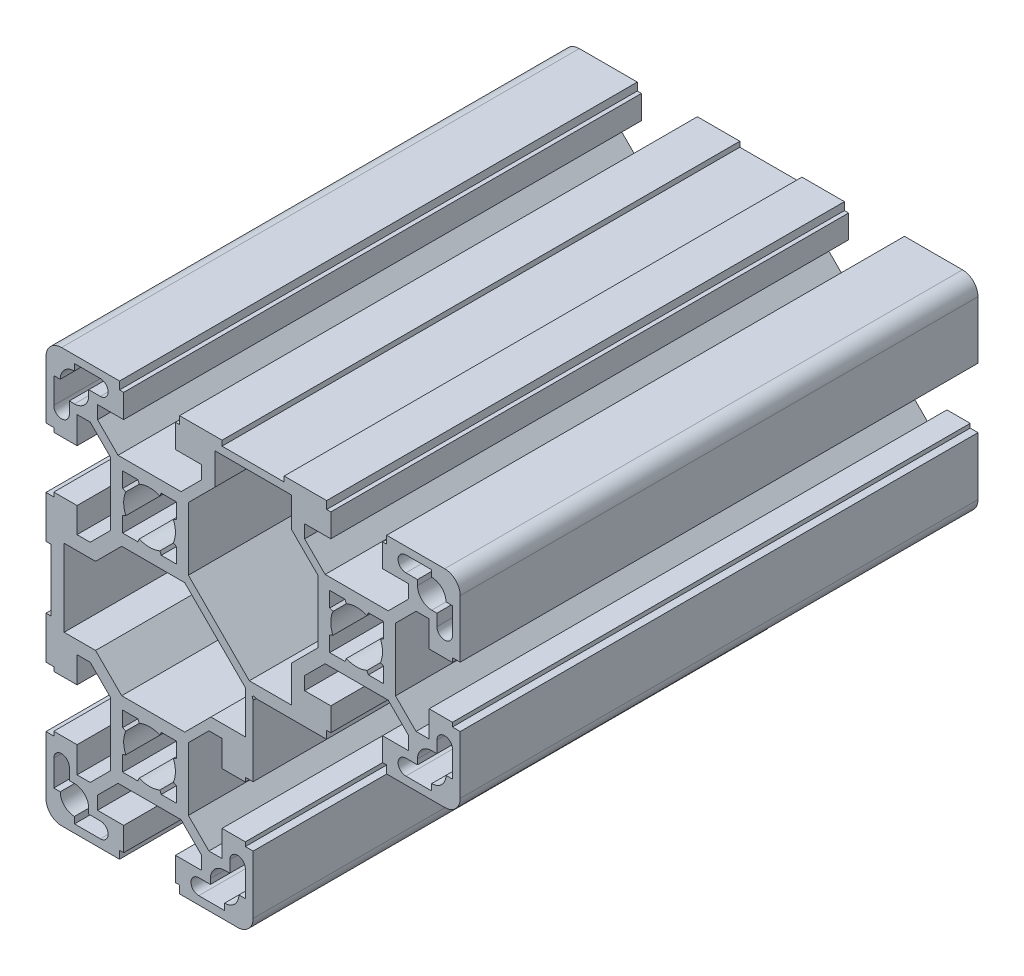
SolidWorks part; units mm, degrees
material "6063-T6"
ref_plane "Front Plane" through (0, 0, 0) normal (0, 0, 1) x (1, 0, 0)
ref_plane "Top Plane" through (0, 0, 0) normal (0, 1, 0) x (1, 0, 0)
ref_plane "Right Plane" through (0, 0, 0) normal (1, 0, 0) x (0, 0, -1)
sketch "Sketch1" plane through (0, 0, 0) normal (0, 0, 1) x (1, 0, 0)
  line L0 (25.9999, 38.9999) -> (14, 38.9999)
  line L1 (19.812, 0) -> (20.0684, 0.2563)
  line L2 (20, -0.5164) -> (19.812, 0)
  line L3 (18.5, -14.1316) -> (20, -14.1316)
  line L4 (20, -25.7315) -> (18.5, -25.7315)
  line L5 (27.4499, 2.3916) -> (19.2677, 2.3916)
  line L6 (12.6384, 37.5406) -> (27.4499, 37.5406)
  line L7 (44.9999, 1.5684) -> (45.7999, 1.5684)
  line L8 (50.0499, 6.0684) -> (44.9999, 6.0684)
  line L9 (44.9999, 33.9999) -> (50.0499, 33.9999)
  line L10 (45.7999, 38.4999) -> (44.9999, 38.4999)
  line L11 (46.0857, 27.4999) -> (33.9141, 27.4999)
  line L12 (33.9141, 12.5684) -> (46.0857, 12.5684)
  line L13 (53.9999, 30.1183) -> (53.9999, 25.0684)
  line L14 (58.4999, 25.0684) -> (58.4999, 25.8684)
  line L15 (47.4999, 13.9826) -> (47.4999, 26.1541)
  line L16 (57.2499, 34.5683) -> (58.4999, 34.5683)
  line L17 (59.9999, 25.8684) -> (59.9999, 36.9999)
  line L18 (58.4999, 34.5683) -> (58.4999, 29.5683)
  line L19 (58.4999, 25.8684) -> (59.9999, 25.8684)
  line L20 (54.4999, 38.5683) -> (54.4999, 37.3183)
  line L21 (56.9999, 39.9999) -> (45.7999, 39.9999)
  line L22 (49.4999, 38.5683) -> (54.4999, 38.5683)
  line L23 (45.7999, 39.9999) -> (45.7999, 38.4999)
  line L24 (51.4641, 30.1183) -> (53.9999, 30.1183)
  line L25 (51.7499, 35.5683) -> (49.4999, 35.5683)
  line L26 (55.4999, 29.5683) -> (55.4999, 31.8183)
  line L27 (55.4999, 31.8183) -> (54.4999, 31.8183)
  line L28 (51.7499, 34.5683) -> (51.7499, 35.5683)
  line L29 (50.0499, 33.9999) -> (50.0499, 31.4642)
  line L30 (50.0499, 31.4642) -> (46.0857, 27.4999)
  line L31 (47.4999, 26.1541) -> (51.4641, 30.1183)
  line L32 (58.4999, 15.0684) -> (53.9999, 15.0684)
  line L33 (58.4999, 5.5684) -> (57.2499, 5.5684)
  line L34 (53.9999, 25.0684) -> (58.4999, 25.0684)
  line L35 (59.9999, 3.0684) -> (59.9999, 14.2684)
  line L36 (59.9999, 14.2684) -> (58.4999, 14.2684)
  line L37 (58.4999, 14.2684) -> (58.4999, 15.0684)
  line L38 (58.4999, 10.5684) -> (58.4999, 5.5684)
  line L39 (51.4641, 10.0184) -> (47.4999, 13.9826)
  line L40 (53.9999, 15.0684) -> (53.9999, 10.0184)
  line L41 (53.9999, 10.0184) -> (51.4641, 10.0184)
  line L42 (45.7999, 0.0684) -> (56.9999, 0.0684)
  line L43 (54.4999, 1.5684) -> (49.4999, 1.5684)
  line L44 (49.4999, 4.5684) -> (51.7499, 4.5684)
  line L45 (54.4999, 8.3184) -> (55.4999, 8.3184)
  line L46 (55.4999, 8.3184) -> (55.4999, 10.5684)
  line L47 (51.7499, 4.5684) -> (51.7499, 5.5684)
  line L48 (54.4999, 2.8184) -> (54.4999, 1.5684)
  line L49 (50.0499, 8.6042) -> (50.0499, 6.0684)
  line L50 (46.0857, 12.5684) -> (50.0499, 8.6042)
  line L51 (45.7999, 1.5684) -> (45.7999, 0.0684)
  line L52 (27.4499, 31.7345) -> (32.4999, 26.6845)
  line L53 (34.1999, 39.9999) -> (25.9999, 39.9999)
  line L54 (29.9499, 33.9999) -> (34.9999, 33.9999)
  line L55 (33.9141, 27.4999) -> (29.9499, 31.4642)
  line L56 (34.9999, 33.9999) -> (34.9999, 38.4999)
  line L57 (44.9999, 38.4999) -> (44.9999, 33.9999)
  line L58 (34.9999, 38.4999) -> (34.1999, 38.4999)
  line L59 (34.1999, 38.4999) -> (34.1999, 39.9999)
  line L60 (25.9999, 39.9999) -> (25.9999, 38.9999)
  line L61 (29.9499, 31.4642) -> (29.9499, 33.9999)
  line L62 (27.4499, 37.5406) -> (27.4499, 31.7345)
  line L63 (29.9499, 8.6042) -> (33.9141, 12.5684)
  line L64 (34.9999, 6.0684) -> (29.9499, 6.0684)
  line L65 (20.5847, 0.0684) -> (34.1999, 0.0684)
  line L66 (41.9931, 24.6539) -> (42.2602, 25.2684)
  line L67 (45.1999, 22.3286) -> (44.5854, 22.0616)
  line L68 (42.2602, 25.2684) -> (45.1999, 25.2684)
  line L69 (45.1999, 25.2684) -> (45.1999, 22.3286)
  line L70 (42.2602, 14.8684) -> (41.9931, 15.4828)
  line L71 (45.1999, 17.8081) -> (45.1999, 14.8684)
  line L72 (44.5854, 18.0752) -> (45.1999, 17.8081)
  line L73 (45.1999, 14.8684) -> (42.2602, 14.8684)
  line L74 (34.7999, 25.2684) -> (37.7396, 25.2684)
  line L75 (37.7396, 25.2684) -> (38.0067, 24.6539)
  line L76 (35.4144, 22.0616) -> (34.7999, 22.3286)
  line L77 (34.7999, 22.3286) -> (34.7999, 25.2684)
  line L78 (37.7396, 14.8684) -> (34.7999, 14.8684)
  line L79 (38.0067, 15.4828) -> (37.7396, 14.8684)
  line L80 (34.7999, 14.8684) -> (34.7999, 17.8081)
  line L81 (34.7999, 17.8081) -> (35.4144, 18.0752)
  line L82 (44.9999, 6.0684) -> (44.9999, 1.5684)
  line L83 (34.9999, 1.5684) -> (34.9999, 6.0684)
  line L84 (34.1999, 1.5684) -> (34.9999, 1.5684)
  line L85 (34.1999, 0.0684) -> (34.1999, 1.5684)
  line L86 (32.4999, 14.5129) -> (27.4499, 9.4629)
  line L87 (32.4999, 26.6845) -> (32.4999, 14.5129)
  line L88 (29.9499, 6.0684) -> (29.9499, 8.6042)
  line L89 (27.4499, 9.4629) -> (27.4499, 2.3916)
  line L90 (20.0684, 0.2563) -> (20.5847, 0.0684)
  line L91 (20, -14.1316) -> (20, -0.5164)
  line L92 (20, -36.9999) -> (20, -25.7315)
  line L93 (-19, 6.0684) -> (-19, -5.9316)
  line L94 (18.5606, 0.8006) -> (18.5606, -7.3816)
  line L95 (-16.5, -7.3816) -> (-16.5, 7.5184)
  line L96 (-10.4287, 7.5184) -> (-5.3787, 12.5684)
  line L97 (-10.05, 33.9315) -> (-5, 33.9315)
  line L98 (-5, 38.4999) -> (-5.8, 38.4999)
  line L99 (6.0858, 27.4315) -> (-6.0858, 27.4315)
  line L100 (7.5, 26.3309) -> (12.6384, 31.4693)
  line L101 (10.05, 31.3957) -> (6.0858, 27.4315)
  line L102 (5, 33.9315) -> (10.05, 33.9315)
  line L103 (14, 39.9999) -> (5.8, 39.9999)
  line L104 (14, 38.9999) -> (14, 39.9999)
  line L105 (10.05, 33.9315) -> (10.05, 31.3957)
  line L106 (12.6384, 31.4693) -> (12.6384, 37.5406)
  line L107 (-5, 33.9315) -> (-5, 38.4999)
  line L108 (5, 38.4999) -> (5, 33.9315)
  line L109 (5.8, 38.4999) -> (5, 38.4999)
  line L110 (5.8, 39.9999) -> (5.8, 38.4999)
  line L111 (6.7929, 12.5684) -> (18.5606, 0.8006)
  line L112 (19.2677, 2.3916) -> (7.5, 14.1594)
  line L113 (7.5, 14.1594) -> (7.5, 26.3309)
  line L114 (2.2603, 25.2684) -> (5.2, 25.2684)
  line L115 (5.2, 22.3286) -> (4.5855, 22.0616)
  line L116 (5.2, 25.2684) -> (5.2, 22.3286)
  line L117 (1.9932, 24.6539) -> (2.2603, 25.2684)
  line L118 (5.2, 14.8684) -> (2.2603, 14.8684)
  line L119 (5.2, 17.8081) -> (5.2, 14.8684)
  line L120 (4.5855, 18.0752) -> (5.2, 17.8081)
  line L121 (2.2603, 14.8684) -> (1.9932, 15.4828)
  line L122 (-2.2603, 25.2684) -> (-1.9932, 24.6539)
  line L123 (-4.5855, 22.0616) -> (-5.2, 22.3286)
  line L124 (-5.2, 25.2684) -> (-2.2603, 25.2684)
  line L125 (-5.2, 22.3286) -> (-5.2, 25.2684)
  line L126 (-1.9932, 15.4828) -> (-2.2603, 14.8684)
  line L127 (-5.2, 14.8684) -> (-5.2, 17.8081)
  line L128 (-5.2, 17.8081) -> (-4.5855, 18.0752)
  line L129 (-2.2603, 14.8684) -> (-5.2, 14.8684)
  line L130 (-5.3787, 12.5684) -> (6.7929, 12.5684)
  line L131 (-18.5, 25.8684) -> (-18.5, 25.0684)
  line L132 (-14, 25.0684) -> (-14, 30.2951)
  line L133 (-7.5, 26.3309) -> (-7.5, 14.1594)
  line L134 (-18.5, 34.5683) -> (-17.25, 34.5683)
  line L135 (-14.5, 37.3183) -> (-14.5, 38.5683)
  line L136 (-5.8, 39.9999) -> (-17, 39.9999)
  line L137 (-14.5, 38.5683) -> (-9.5, 38.5683)
  line L138 (-5.8, 38.4999) -> (-5.8, 39.9999)
  line L139 (-14, 30.2951) -> (-11.4642, 30.2951)
  line L140 (-9.5, 35.5683) -> (-11.75, 35.5683)
  line L141 (-10.05, 31.3957) -> (-10.05, 33.9315)
  line L142 (-6.0858, 27.4315) -> (-10.05, 31.3957)
  line L143 (-11.4642, 30.2951) -> (-7.5, 26.3309)
  line L144 (-15.5, 31.8183) -> (-15.5, 29.5683)
  line L145 (-14.5, 31.8183) -> (-15.5, 31.8183)
  line L146 (-11.75, 35.5683) -> (-11.75, 34.5683)
  line L147 (-20, 36.9999) -> (-20, 25.8684)
  line L148 (-18.5, 29.5683) -> (-18.5, 34.5683)
  line L149 (-20, 25.8684) -> (-18.5, 25.8684)
  line L150 (-14, 15.0684) -> (-18.5, 15.0684)
  line L151 (-18.5, 25.0684) -> (-14, 25.0684)
  line L152 (-14, 10.1952) -> (-14, 15.0684)
  line L153 (-7.5, 14.1594) -> (-11.4642, 10.1952)
  line L154 (-11.4642, 10.1952) -> (-14, 10.1952)
  line L155 (-16.5, 7.5184) -> (-10.4287, 7.5184)
  line L156 (-20, 14.2684) -> (-20, 6.0684)
  line L157 (-18.5, 14.2684) -> (-20, 14.2684)
  line L158 (-18.5, 15.0684) -> (-18.5, 14.2684)
  line L159 (-20, 6.0684) -> (-19, 6.0684)
  line L160 (-5.8, -38.4999) -> (-5, -38.4999)
  line L161 (-5, -33.9315) -> (-10.05, -33.9315)
  line L162 (-5.3787, -12.4316) -> (-10.4287, -7.3816)
  line L163 (-6.0858, -27.4315) -> (6.0858, -27.4315)
  line L164 (7.5, -26.0173) -> (7.5, -13.8458)
  line L165 (14, -24.9315) -> (14, -29.9815)
  line L166 (18.5, -25.7315) -> (18.5, -24.9315)
  line L167 (11.8429, -7.3816) -> (6.7929, -12.4316)
  line L168 (14, -9.8816) -> (14, -14.9316)
  line L169 (7.5, -13.8458) -> (11.4642, -9.8816)
  line L170 (11.4642, -9.8816) -> (14, -9.8816)
  line L171 (18.5606, -7.3816) -> (11.8429, -7.3816)
  line L172 (14, -14.9316) -> (18.5, -14.9316)
  line L173 (18.5, -14.9316) -> (18.5, -14.1316)
  line L174 (18.5, -24.9315) -> (14, -24.9315)
  line L175 (6.7929, -12.4316) -> (-5.3787, -12.4316)
  line L176 (2.2603, -14.7316) -> (5.2, -14.7316)
  line L177 (5.2, -14.7316) -> (5.2, -17.6713)
  line L178 (5.2, -17.6713) -> (4.5855, -17.9384)
  line L179 (1.9932, -15.346) -> (2.2603, -14.7316)
  line L180 (5.2, -25.1315) -> (2.2603, -25.1315)
  line L181 (4.5855, -21.9248) -> (5.2, -22.1918)
  line L182 (5.2, -22.1918) -> (5.2, -25.1315)
  line L183 (2.2603, -25.1315) -> (1.9932, -24.5171)
  line L184 (-2.2603, -14.7316) -> (-1.9932, -15.346)
  line L185 (-5.2, -17.6713) -> (-5.2, -14.7316)
  line L186 (-5.2, -14.7316) -> (-2.2603, -14.7316)
  line L187 (-4.5855, -17.9384) -> (-5.2, -17.6713)
  line L188 (-1.9932, -24.5171) -> (-2.2603, -25.1315)
  line L189 (-5.2, -22.1918) -> (-4.5855, -21.9248)
  line L190 (-2.2603, -25.1315) -> (-5.2, -25.1315)
  line L191 (-5.2, -25.1315) -> (-5.2, -22.1918)
  line L192 (5.8, -39.9999) -> (17, -39.9999)
  line L193 (10.05, -33.9315) -> (5, -33.9315)
  line L194 (6.0858, -27.4315) -> (10.05, -31.3957)
  line L195 (14.5, -37.1815) -> (14.5, -38.4315)
  line L196 (14, -29.9815) -> (11.4642, -29.9815)
  line L197 (15.5, -31.6815) -> (15.5, -29.4315)
  line L198 (18.5, -29.4315) -> (18.5, -34.4315)
  line L199 (18.5, -34.4315) -> (17.25, -34.4315)
  line L200 (14.5, -31.6815) -> (15.5, -31.6815)
  line L201 (10.05, -31.3957) -> (10.05, -33.9315)
  line L202 (11.4642, -29.9815) -> (7.5, -26.0173)
  line L203 (9.5, -35.4315) -> (11.75, -35.4315)
  line L204 (11.75, -35.4315) -> (11.75, -34.4315)
  line L205 (14.5, -38.4315) -> (9.5, -38.4315)
  line L206 (-5, -38.4999) -> (-5, -33.9315)
  line L207 (5, -33.9315) -> (5, -38.4999)
  line L208 (5, -38.4999) -> (5.8, -38.4999)
  line L209 (5.8, -38.4999) -> (5.8, -39.9999)
  line L210 (-18.5, -24.9315) -> (-18.5, -25.7315)
  line L211 (-14, -29.9815) -> (-14, -24.9315)
  line L212 (-7.5, -13.8458) -> (-7.5, -26.0173)
  line L213 (-14, -24.9315) -> (-18.5, -24.9315)
  line L214 (-18.5, -14.9315) -> (-14, -14.9315)
  line L215 (-11.4642, -9.8816) -> (-7.5, -13.8458)
  line L216 (-14, -14.9315) -> (-14, -9.8816)
  line L217 (-14, -9.8816) -> (-11.4642, -9.8816)
  line L218 (-10.4287, -7.3816) -> (-16.5, -7.3816)
  line L219 (-20, -5.9316) -> (-20, -14.1316)
  line L220 (-19, -5.9316) -> (-20, -5.9316)
  line L221 (-20, -14.1316) -> (-18.5, -14.1316)
  line L222 (-18.5, -14.1316) -> (-18.5, -14.9315)
  line L223 (-17.25, -34.4315) -> (-18.5, -34.4315)
  line L224 (-14.5, -38.4315) -> (-14.5, -37.1815)
  line L225 (-11.4642, -29.9815) -> (-14, -29.9815)
  line L226 (-11.75, -35.4315) -> (-9.5, -35.4315)
  line L227 (-10.05, -33.9315) -> (-10.05, -31.3957)
  line L228 (-10.05, -31.3957) -> (-6.0858, -27.4315)
  line L229 (-7.5, -26.0173) -> (-11.4642, -29.9815)
  line L230 (-15.5, -29.4315) -> (-15.5, -31.6815)
  line L231 (-15.5, -31.6815) -> (-14.5, -31.6815)
  line L232 (-11.75, -34.4315) -> (-11.75, -35.4315)
  line L233 (-17, -39.9999) -> (-5.8, -39.9999)
  line L234 (-9.5, -38.4315) -> (-14.5, -38.4315)
  line L235 (-5.8, -39.9999) -> (-5.8, -38.4999)
  line L236 (-20, -25.7315) -> (-20, -36.9999)
  line L237 (-18.5, -34.4315) -> (-18.5, -29.4315)
  line L238 (-18.5, -25.7315) -> (-20, -25.7315)
  line L239 (0, 54.7953) -> (0, -54.7953) construction
  line L240 (-40.4366, 0) -> (40.4366, 0) construction
  arc A0 (17, -39.9999) -> (20, -36.9999) centre (17, -36.9999) ccw
  arc A1 (59.9999, 36.9999) -> (56.9999, 39.9999) centre (56.9999, 36.9999) ccw
  arc A2 (55.4999, 29.5683) -> (58.4999, 29.5683) centre (56.9999, 29.5683) ccw
  arc A3 (49.4999, 38.5683) -> (49.4999, 35.5683) centre (49.4999, 37.0683) ccw
  arc A4 (51.7499, 34.5683) -> (54.4999, 31.8183) centre (54.4999, 34.5683) ccw
  arc A5 (57.2499, 34.5683) -> (54.4999, 37.3183) centre (54.4999, 34.5683) ccw
  arc A6 (58.4999, 10.5684) -> (55.4999, 10.5684) centre (56.9999, 10.5684) ccw
  arc A7 (56.9999, 0.0684) -> (59.9999, 3.0684) centre (56.9999, 3.0684) ccw
  arc A8 (54.4999, 8.3184) -> (51.7499, 5.5684) centre (54.4999, 5.5684) ccw
  arc A9 (54.4999, 2.8184) -> (57.2499, 5.5684) centre (54.4999, 5.5684) ccw
  arc A10 (49.4999, 4.5684) -> (49.4999, 1.5684) centre (49.4999, 3.0684) ccw
  arc A11 (38.0067, 15.4828) -> (41.9931, 15.4828) centre (39.9999, 20.0684) ccw
  arc A12 (41.9931, 24.6539) -> (38.0067, 24.6539) centre (39.9999, 20.0684) ccw
  arc A13 (44.5854, 18.0752) -> (44.5854, 22.0616) centre (39.9999, 20.0684) ccw
  arc A14 (35.4144, 22.0616) -> (35.4144, 18.0752) centre (39.9999, 20.0684) ccw
  arc A15 (-1.9932, 15.4828) -> (1.9932, 15.4828) centre (0, 20.0684) ccw
  arc A16 (1.9932, 24.6539) -> (-1.9932, 24.6539) centre (0, 20.0684) ccw
  arc A17 (4.5855, 18.0752) -> (4.5855, 22.0616) centre (0, 20.0684) ccw
  arc A18 (-4.5855, 22.0616) -> (-4.5855, 18.0752) centre (0, 20.0684) ccw
  arc A19 (-17, 39.9999) -> (-20, 36.9999) centre (-17, 36.9999) ccw
  arc A20 (-18.5, 29.5683) -> (-15.5, 29.5683) centre (-17, 29.5683) ccw
  arc A21 (-9.5, 35.5683) -> (-9.5, 38.5683) centre (-9.5, 37.0683) ccw
  arc A22 (-14.5, 31.8183) -> (-11.75, 34.5683) centre (-14.5, 34.5683) ccw
  arc A23 (-14.5, 37.3183) -> (-17.25, 34.5683) centre (-14.5, 34.5683) ccw
  arc A24 (-1.9932, -24.5171) -> (1.9932, -24.5171) centre (0, -19.9316) ccw
  arc A25 (1.9932, -15.346) -> (-1.9932, -15.346) centre (0, -19.9316) ccw
  arc A26 (4.5855, -21.9248) -> (4.5855, -17.9384) centre (0, -19.9316) ccw
  arc A27 (-4.5855, -17.9384) -> (-4.5855, -21.9248) centre (0, -19.9316) ccw
  arc A28 (9.5, -35.4315) -> (9.5, -38.4315) centre (9.5, -36.9315) ccw
  arc A29 (14.5, -31.6815) -> (11.75, -34.4315) centre (14.5, -34.4315) ccw
  arc A30 (18.5, -29.4315) -> (15.5, -29.4315) centre (17, -29.4315) ccw
  arc A31 (14.5, -37.1815) -> (17.25, -34.4315) centre (14.5, -34.4315) ccw
  arc A32 (-20, -36.9999) -> (-17, -39.9999) centre (-17, -36.9999) ccw
  arc A33 (-15.5, -29.4315) -> (-18.5, -29.4315) centre (-17, -29.4315) ccw
  arc A34 (-9.5, -38.4315) -> (-9.5, -35.4315) centre (-9.5, -36.9315) ccw
  arc A35 (-11.75, -34.4315) -> (-14.5, -31.6815) centre (-14.5, -34.4315) ccw
  arc A36 (-17.25, -34.4315) -> (-14.5, -37.1815) centre (-14.5, -34.4315) ccw
  dimension "D3" = 10
  dimension "D1" = 39.9999
  dimension "D2" = 79.9998
  dimension "D4" = 10
  dimension "D5" = 10
  dimension "D6" = 10
  dimension "D7" = 10
  dimension "D8" = 10
  dimension "D9" = 10
extrude "Extrude1" add sketch "Sketch1" against normal blind 100
